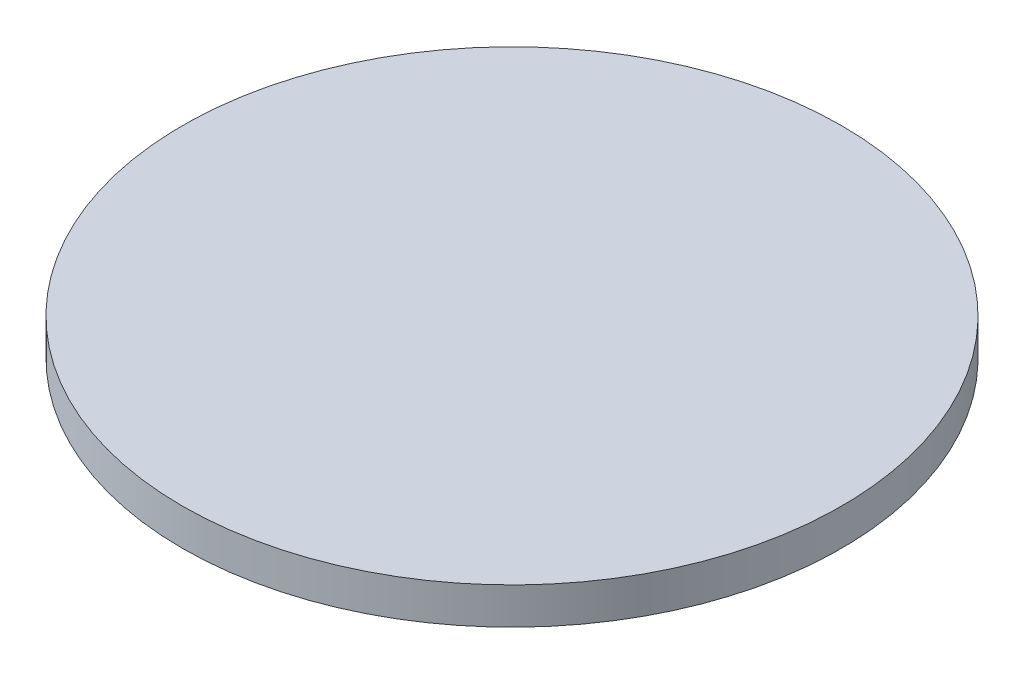
SolidWorks part; units mm, degrees
ref_plane "Front Plane" through (0, 0, 0) normal (0, 0, 1) x (1, 0, 0)
ref_plane "Top Plane" through (0, 0, 0) normal (0, 1, 0) x (1, 0, 0)
ref_plane "Right Plane" through (0, 0, 0) normal (1, 0, 0) x (0, 0, -1)
sketch "Sketch1" plane through (0, 0, 0) normal (0, 1, 0) x (1, 0, 0)
  circle A0 centre (0, 0) radius 457.2
  dimension "D1" = 914.4
extrude "Boss-Extrude1" add sketch "Sketch1" along normal blind 50.8
